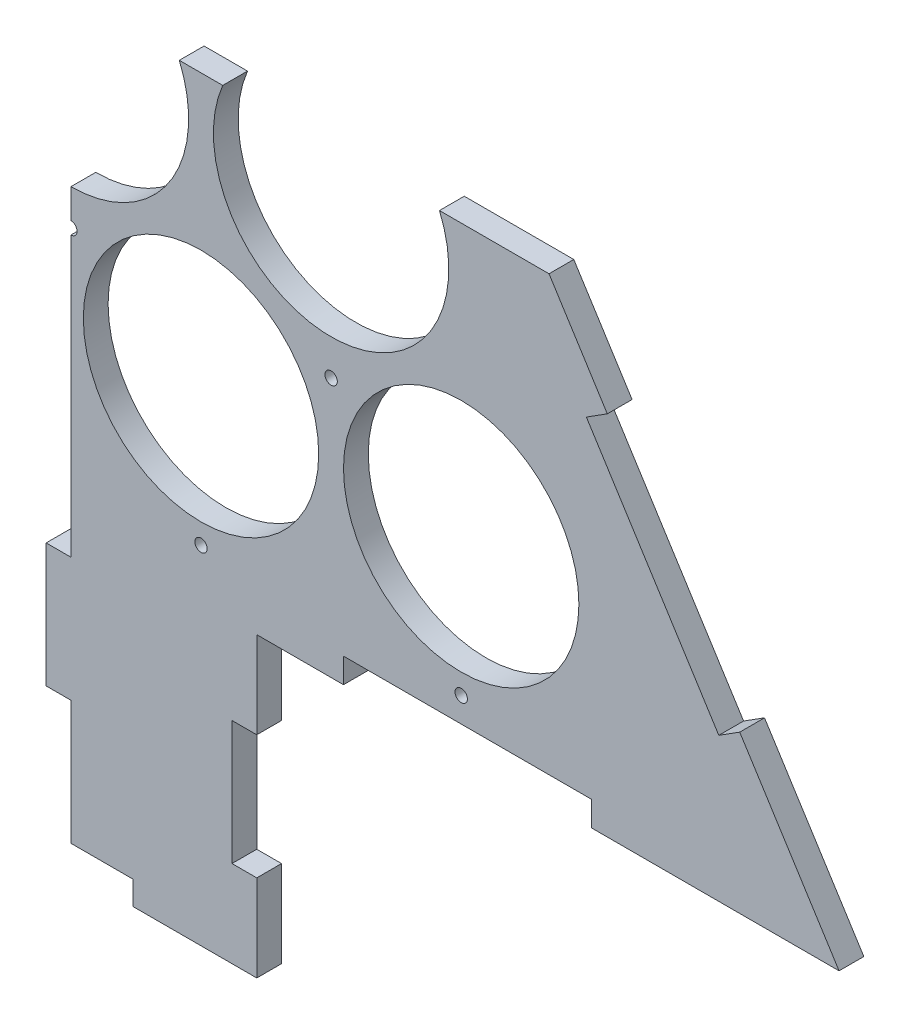
SolidWorks part; units mm, degrees
ref_plane "Plan de face" through (0, 0, 0) normal (0, 0, 1) x (1, 0, 0)
ref_plane "Plan de dessus" through (0, 0, 0) normal (0, 1, 0) x (1, 0, 0)
ref_plane "Plan de droite" through (0, 0, 0) normal (1, 0, 0) x (0, 0, -1)
sketch "Esquisse1" plane through (0, 0, 0) normal (0, 0, 1) x (1, 0, 0)
  line L0 (0, 0) -> (-371.1464, 0) construction
  line L1 (0, 0) -> (478.5179, 0) construction
  line L2 (0, 0) -> (0, 90.9327) construction
  line L3 (0, 90.9327) -> (-157.5, 90.9327) construction
  line L4 (0, 90.9327) -> (157.5, 90.9327) construction
  line L5 (0, 90.9327) -> (0, 181.8653) construction
  line L6 (0, 181.8653) -> (-52.5, 181.8653) construction
  line L7 (0, 181.8653) -> (52.5, 181.8653) construction
  line L8 (0, 181.8653) -> (0, 363.4062) construction
  line L9 (-310, -75.6429) -> (0, 414.5612)
  line L10 (0, 414.5612) -> (310, -75.6429)
  line L11 (310, -75.6429) -> (-310, -75.6429)
  circle A0 centre (-157.5, 0) radius 47.5
  circle A1 centre (-52.5, 0) radius 47.5
  circle A2 centre (52.5, 0) radius 47.5
  circle A3 centre (157.5, 0) radius 47.5
  circle A4 centre (-105, 90.9327) radius 47.5
  circle A5 centre (0, 90.9327) radius 47.5
  circle A6 centre (105, 90.9327) radius 47.5
  circle A7 centre (-52.5, 181.8653) radius 47.5
  circle A8 centre (52.5, 181.8653) radius 47.5
  circle A9 centre (0, 272.798) radius 47.5
  dimension "D1" = 95
  dimension "D2" = 95
  dimension "D3" = 95
  dimension "D4" = 95
  dimension "D5" = 105
  dimension "D6" = 52.5
  dimension "D7" = 52.5
  dimension "D8" = 105
  dimension "D9" = 95
  dimension "D10" = 95
  dimension "D11" = 95
  dimension "D12" = 105
  dimension "D13" = 105
  dimension "D14" = 105
  dimension "D15" = 95
  dimension "D16" = 95
  dimension "D17" = 105
  dimension "D18" = 52.5
  dimension "D19" = 52.5
  dimension "D20" = 95
  dimension "D21" = 105
  dimension "D22" = 80
  dimension "D23" = 620
  dimension "D24" = 580
  dimension "D25" = 0
  dimension "D26" = 580
extrude "Boss.-Extru.1" add sketch "Esquisse1" along normal blind 10
sketch "Esquisse3" plane through (0, 0, 10) normal (0, 0, 1) x (1, 0, 0)
  line L10 (-269.9138, -12.2544) -> (-261.462, -17.5992)
  line L15 (0, 414.5612) -> (-310, -75.6429) construction
  line L16 (-261.462, -17.5992) -> (-208.0137, 66.9187)
  line L17 (-208.0137, 66.9187) -> (-216.4655, 72.2635)
  line L18 (-216.4655, 72.2635) -> (-269.9138, -12.2544)
  line L19 (-181.7241, 127.2002) -> (-173.2723, 121.8554)
  line L20 (-173.2723, 121.8554) -> (-119.8241, 206.3733)
  line L21 (-119.8241, 206.3733) -> (-128.2759, 211.7181)
  line L22 (-128.2759, 211.7181) -> (-181.7241, 127.2002)
  line L23 (-93.5345, 266.6548) -> (-85.0827, 261.31)
  line L24 (-85.0827, 261.31) -> (-31.6344, 345.8279)
  line L25 (-31.6344, 345.8279) -> (-40.0862, 351.1727)
  line L26 (-40.0862, 351.1727) -> (-93.5345, 266.6548)
  line L27 (269.9138, -12.2544) -> (261.462, -17.5992)
  line L28 (310, -75.6429) -> (0, 414.5612) construction
  line L29 (261.462, -17.5992) -> (208.0137, 66.9187)
  line L30 (208.0137, 66.9187) -> (216.4655, 72.2635)
  line L31 (216.4655, 72.2635) -> (269.9138, -12.2544)
  line L32 (181.7241, 127.2002) -> (173.2723, 121.8554)
  line L33 (173.2723, 121.8554) -> (119.8241, 206.3733)
  line L34 (119.8241, 206.3733) -> (128.2759, 211.7181)
  line L35 (128.2759, 211.7181) -> (181.7241, 127.2002)
  line L36 (93.5345, 266.6548) -> (85.0827, 261.31)
  line L37 (85.0827, 261.31) -> (31.6344, 345.8279)
  line L38 (31.6344, 345.8279) -> (40.0862, 351.1727)
  line L39 (40.0862, 351.1727) -> (93.5345, 266.6548)
  line L40 (-310, -75.6429) -> (310, -75.6429) construction
  line L41 (-210, -75.6429) -> (-110, -75.6429)
  line L42 (-210, -75.6429) -> (-210, -65.6429)
  line L43 (-210, -65.6429) -> (-110, -65.6429)
  line L44 (-110, -75.6429) -> (-110, -65.6429)
  line L45 (0, 0) -> (0, -75.6429) construction
  line L46 (210, -65.6429) -> (110, -65.6429)
  line L47 (110, -75.6429) -> (110, -65.6429)
  line L48 (210, -75.6429) -> (110, -75.6429)
  line L49 (210, -75.6429) -> (210, -65.6429)
  dimension "D3" = 100
  dimension "D4" = 10
  dimension "D5" = 100
  dimension "D10" = 10
  dimension "D11" = 100
  dimension "D12" = 10
  dimension "D13" = 100
  dimension "D14" = 10
  dimension "D15" = 100
  dimension "D16" = 75
  dimension "D17" = 75
  dimension "D18" = 65
  dimension "D19" = 100
  dimension "D20" = 10
  dimension "D21" = 10
  dimension "D22" = 100
  dimension "D23" = 75
  dimension "D24" = 65
  dimension "D25" = 100
  dimension "D26" = 10
  dimension "D27" = 75
extrude "Enlèv. mat.-Extru.1" cut sketch "Esquisse3" against normal through all
sketch "Esquisse4" plane through (0, 0, 10) normal (0, 0, 1) x (1, 0, 0)
  line L0 (-110, -65.6429) -> (-210, -65.6429) construction
  circle A0 centre (-157.5, -55.6429) radius 2.5
  circle A3 centre (-52.5, -55.6429) radius 2.5
  circle A4 centre (52.5, -55.6429) radius 2.5
  circle A5 centre (157.5, -55.6429) radius 2.5
  circle A6 centre (-105, 29.0474) radius 2.5
  circle A8 centre (-157.5, 0) radius 47.5 construction
  circle A10 centre (-52.5, 0) radius 47.5 construction
  circle A12 centre (0, 29.0474) radius 2.5
  circle A13 centre (105, 29.0474) radius 2.5
  circle A14 centre (-52.5, 119.98) radius 2.5
  circle A15 centre (-105, 90.9327) radius 47.5 construction
  circle A16 centre (0, 90.9327) radius 47.5 construction
  circle A17 centre (52.5, 119.98) radius 2.5
  circle A18 centre (0, 210.9127) radius 2.5
  circle A19 centre (52.5, 181.8653) radius 47.5 construction
  circle A20 centre (-52.5, 181.8653) radius 47.5 construction
  dimension "D1" = 5
  dimension "D2" = 10
  dimension "D3" = 4
  dimension "D4" = 5
  dimension "D5" = 60
  dimension "D6" = 60
  dimension "D7" = 3
  dimension "D8" = 5
  dimension "D9" = 60
  dimension "D10" = 60
  dimension "D12" = 5
  dimension "D13" = 60
  dimension "D14" = 60
  dimension "D11" = 2
extrude "Enlèv. mat.-Extru.2" cut sketch "Esquisse4" against normal through all
sketch "Esquisse6" plane through (0, 0, 10) normal (0, 0, 1) x (1, 0, 0)
  line L0 (-110, -75.6429) -> (110, -75.6429) construction
  line L1 (-75, -75.6429) -> (75, -75.6429)
  line L2 (-75, -75.6429) -> (-75, -195.6429)
  line L3 (-75, -195.6429) -> (75, -195.6429)
  line L4 (75, -75.6429) -> (75, -195.6429)
  dimension "D1" = 150
  dimension "D2" = 120
  dimension "D3" = 75
extrude "Boss.-Extru.2" add sketch "Esquisse6" against normal blind 10
sketch "Esquisse7" plane through (0, 0, 10) normal (0, 0, 1) x (1, 0, 0)
  line L0 (-75, -75.6429) -> (-75, -195.6429) construction
  line L1 (-75, -110.6429) -> (-65, -110.6429)
  line L2 (-75, -110.6429) -> (-75, -160.6429)
  line L3 (-75, -160.6429) -> (-65, -160.6429)
  line L4 (-65, -110.6429) -> (-65, -160.6429)
  line L5 (-75, -195.6429) -> (75, -195.6429) construction
  line L6 (-25, -195.6429) -> (25, -195.6429)
  line L7 (-25, -195.6429) -> (-25, -186.0721)
  line L8 (-25, -186.0721) -> (25, -186.0721)
  line L9 (25, -195.6429) -> (25, -186.0721)
  line L10 (75, -195.6429) -> (75, -75.6429) construction
  line L11 (75, -160.6429) -> (65, -160.6429)
  line L12 (75, -160.6429) -> (75, -110.6429)
  line L13 (75, -110.6429) -> (65, -110.6429)
  line L14 (65, -160.6429) -> (65, -110.6429)
  line L15 (75, -75.6429) -> (110, -75.6429) construction
  line L16 (-110, -75.6429) -> (-75, -75.6429) construction
  dimension "D1" = 10
  dimension "D2" = 10
  dimension "D3" = 50
  dimension "D4" = 50
  dimension "D5" = 35
  dimension "D6" = 35
  dimension "D7" = 50
  dimension "D8" = 50
extrude "Enlèv. mat.-Extru.3" cut sketch "Esquisse7" against normal blind 10
sketch "Esquisse8" plane through (0, 0, 10) normal (0, 0, 1) x (1, 0, 0)
  line L0 (0, -217.3468) -> (0, 109.4612)
  line L1 (0, 414.5612) -> (-356.6577, 414.5612)
  line L3 (0, -217.3468) -> (-356.6577, -217.3468)
  line L4 (-356.6577, 414.5612) -> (-356.6577, -217.3468)
  line L5 (0, 414.5612) -> (292.5693, 414.5612)
  line L7 (0, 109.4612) -> (292.5693, 109.4612)
  line L8 (292.5693, 414.5612) -> (292.5693, 109.4612)
  dimension "D1" = 305.1
extrude "Enlèv. mat.-Extru.4" cut sketch "Esquisse8" against normal blind 10
sketch "Esquisse9" plane through (0, 0, 10) normal (0, 0, 1) x (1, 0, 0)
  line L0 (0, -186.0721) -> (0, 26.5474) construction
  line L1 (0, -86.0721) -> (-10, -86.0721)
  line L2 (0, -86.0721) -> (0, -136.0721)
  line L3 (0, -136.0721) -> (-10, -136.0721)
  line L4 (-10, -86.0721) -> (-10, -136.0721)
  line L5 (25, -186.0721) -> (0, -186.0721) construction
  point P8 (12.5, -186.0721)
  dimension "D1" = 10
  dimension "D2" = 50
  dimension "D3" = 50
extrude "Boss.-Extru.3" add sketch "Esquisse9" against normal blind 10
